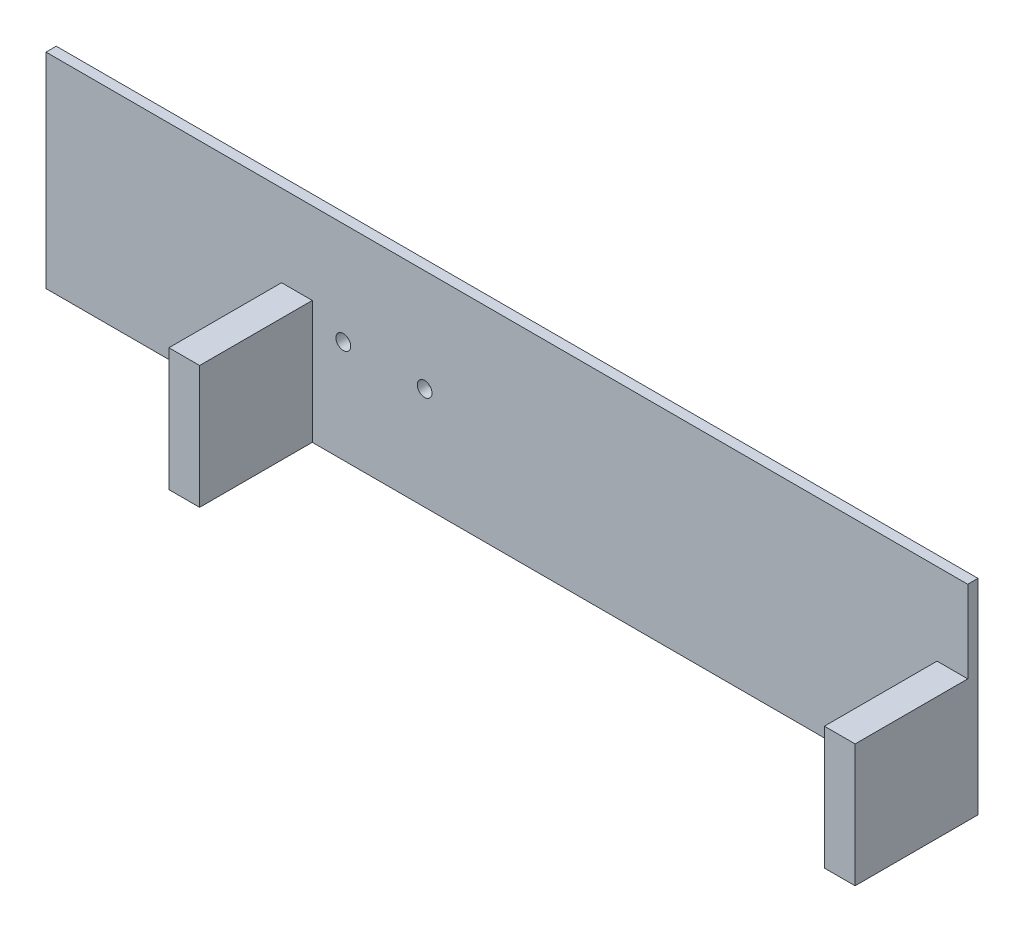
SolidWorks part; units mm, degrees
ref_plane "Front Plane" through (0, 0, 0) normal (0, 0, 1) x (1, 0, 0)
ref_plane "Top Plane" through (0, 0, 0) normal (0, 1, 0) x (1, 0, 0)
ref_plane "Right Plane" through (0, 0, 0) normal (1, 0, 0) x (0, 0, -1)
sketch "Sketch1" plane through (0, 0, 0) normal (0, 0, 1) x (1, 0, 0)
  line L1 (225, -50) -> (-225, -50)
  line L2 (225, -50) -> (225, 50)
  line L3 (225, 50) -> (-225, 50)
  line L4 (-225, -50) -> (-225, 50)
  line L5 (225, -50) -> (-225, 50) construction
  line L6 (225, 50) -> (-225, -50) construction
  point P0 (0, 0)
  dimension "D1" = 100
  dimension "D2" = 450
extrude "Boss-Extrude1" add sketch "Sketch1" along normal blind 5
sketch "Sketch2" plane through (0, 0, 5) normal (0, 0, 1) x (1, 0, 0)
  line L1 (210, 10) -> (225, 10)
  line L2 (210, 10) -> (210, -50)
  line L3 (210, -50) -> (225, -50)
  line L4 (225, 10) -> (225, -50)
  line L5 (-225, -50) -> (225, -50) construction
  line L6 (-110, 10) -> (-95, 10)
  line L7 (-110, 10) -> (-110, -50)
  line L8 (-110, -50) -> (-95, -50)
  line L9 (-95, 10) -> (-95, -50)
  dimension "D1" = 15
  dimension "D2" = 305
  dimension "D3" = 60
extrude "Boss-Extrude2" add sketch "Sketch2" along normal blind 55
sketch "Sketch3" plane through (0, 0, 5) normal (0, 0, 1) x (1, 0, 0)
  line L0 (-60, 0) -> (-60, 17.868) construction
  line L1 (-95, 10) -> (-95, -50) construction
  circle A0 centre (-79.85, 0) radius 3.6
  circle A1 centre (-40.15, 0) radius 3.6
  point P4 (0, 0)
  dimension "D2" = 7.2
  dimension "D3" = 7.2
  dimension "D1" = 39.7
  dimension "D4" = 35
extrude "Cut-Extrude1" cut sketch "Sketch3" against normal through all both and the other way through all
